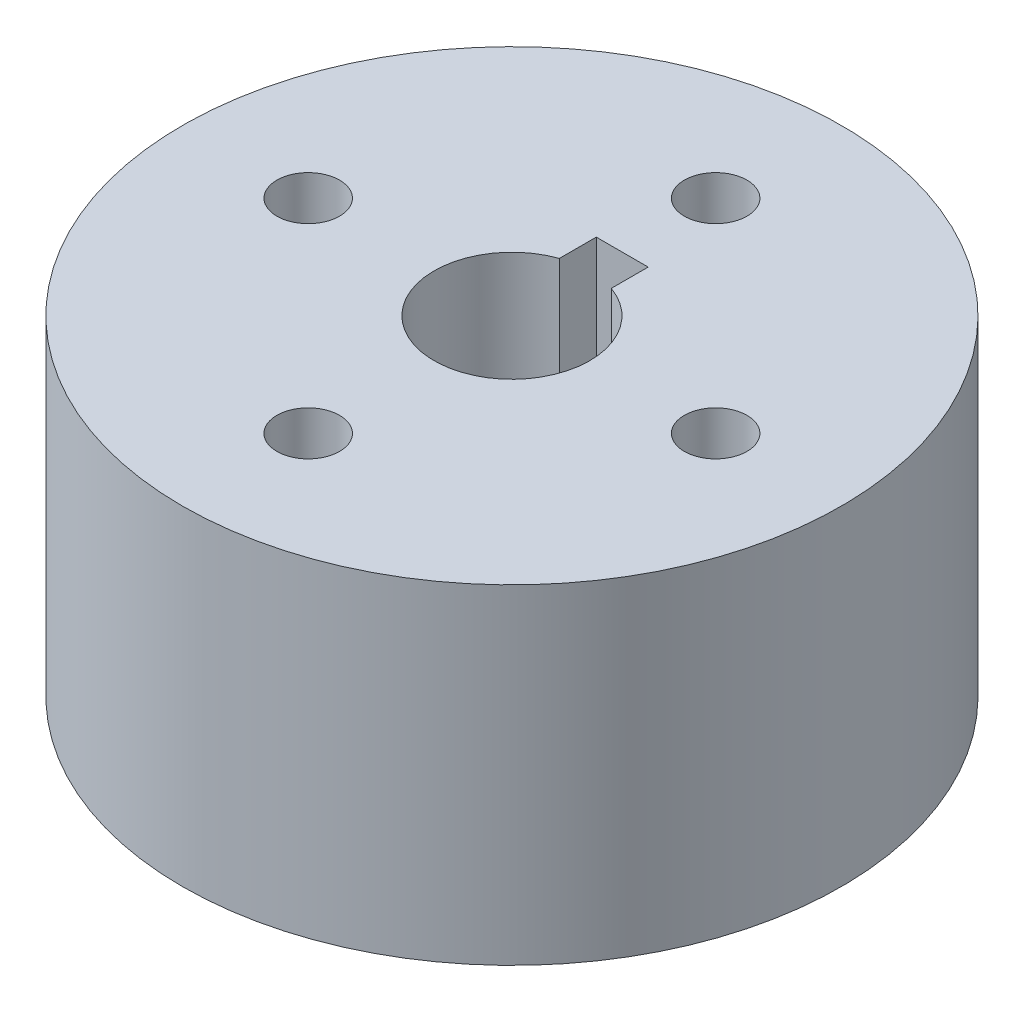
SolidWorks part; units mm, degrees
ref_plane "Front Plane" through (0, 0, 0) normal (0, 0, 1) x (1, 0, 0)
ref_plane "Top Plane" through (0, 0, 0) normal (0, 1, 0) x (1, 0, 0)
ref_plane "Right Plane" through (0, 0, 0) normal (1, 0, 0) x (0, 0, -1)
sketch "Sketch1" plane through (0, 0, 0) normal (0, 1, 0) x (1, 0, 0)
  circle A0 centre (0, 0) radius 25.4
  circle A1 centre (0, 0) radius 6
  dimension "D1" = 50.8
  dimension "D2" = 12
extrude "Boss-Extrude1" add sketch "Sketch1" along normal blind 25.4
sketch "Sketch2" plane through (0, 25.4, 0) normal (0, 1, 0) x (1, 0, 0)
  line L1 (-2, 8.5) -> (2, 8.5)
  line L2 (-2, 8.5) -> (-2, 3.5)
  line L3 (-2, 3.5) -> (2, 3.5)
  line L4 (2, 8.5) -> (2, 3.5)
  circle A0 centre (0, 0) radius 6 construction
  point P4 (0, -6)
  point P5 (0, 3.5)
  point P8 (0, 0)
  dimension "D1" = 4
  dimension "D2" = 5
  dimension "D3" = 9.5
extrude "Cut-Extrude1" cut sketch "Sketch2" against normal blind 16.825
sketch "Sketch3" plane through (0, 0, 0) normal (0, -1, 0) x (1, 0, 0)
  line L0 (0, 0) -> (0, -27.8846) construction
  line L1 (0, 0) -> (-33.7374, 0) construction
  line L2 (0, 0) -> (32.557, 0) construction
  line L3 (0, 0) -> (0, 31.4) construction
  circle A4 centre (0, 0) radius 15.7 construction
  circle A5 centre (0, -15.7) radius 2.413
  circle A6 centre (-15.7, 0) radius 2.413
  circle A7 centre (0, 15.7) radius 2.413
  circle A8 centre (15.7, 0) radius 2.413
  dimension "D1" = 31.4
  dimension "D2" = 4.826
extrude "Cut-Extrude2" cut sketch "Sketch3" against normal through all
